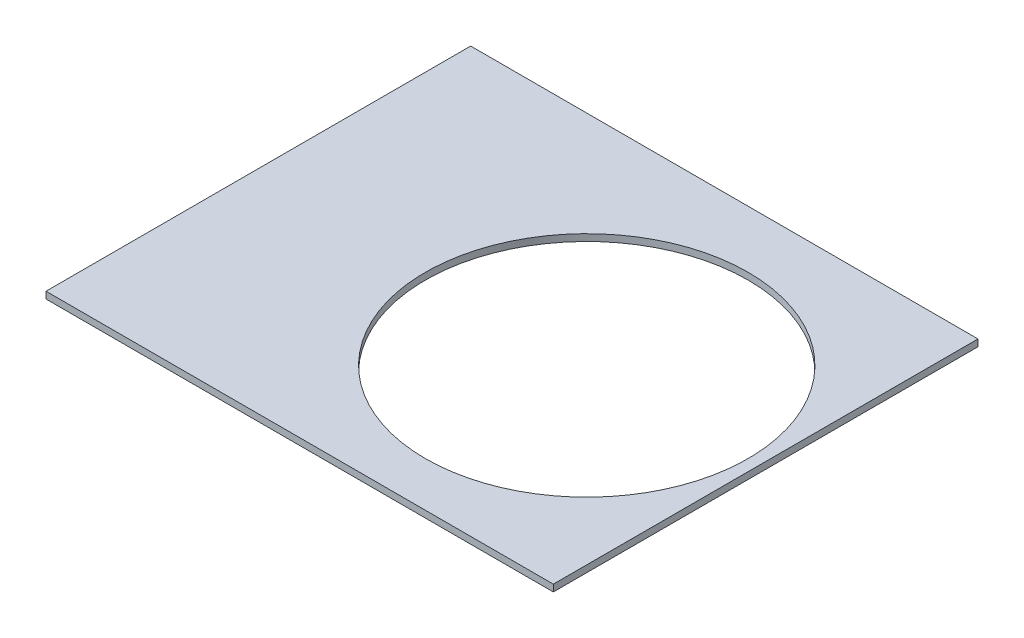
SolidWorks part; units mm, degrees
ref_plane "Front Plane" through (0, 0, 0) normal (0, 0, 1) x (1, 0, 0)
ref_plane "Top Plane" through (0, 0, 0) normal (0, 1, 0) x (1, 0, 0)
ref_plane "Right Plane" through (0, 0, 0) normal (1, 0, 0) x (0, 0, -1)
sketch "Sketch1" plane through (0, 0, 0) normal (0, 1, 0) x (1, 0, 0)
  line L1 (44.8, -37.5) -> (-44.8, -37.5)
  line L2 (44.8, -37.5) -> (44.8, 37.5)
  line L3 (44.8, 37.5) -> (-44.8, 37.5)
  line L4 (-44.8, -37.5) -> (-44.8, 37.5)
  line L5 (44.8, -37.5) -> (-44.8, 37.5) construction
  line L6 (44.8, 37.5) -> (-44.8, -37.5) construction
  point P0 (0, 0)
  dimension "D1" = 89.6
  dimension "D2" = 75
extrude "Boss-Extrude1" add sketch "Sketch1" along normal blind 1.2
sketch "Sketch2" plane through (0, 1.2, 0) normal (0, 1, 0) x (1, 0, 0)
  line L0 (44.8, -37.5) -> (44.8, 37.5) construction
  line L1 (-44.8, -37.5) -> (44.8, -37.5) construction
  circle A0 centre (14.3, -1.1) radius 28.5
  dimension "D3" = 57
  dimension "D1" = 30.5
  dimension "D2" = 36.4
extrude "Cut-Extrude1" cut sketch "Sketch2" against normal through all both and the other way through all
